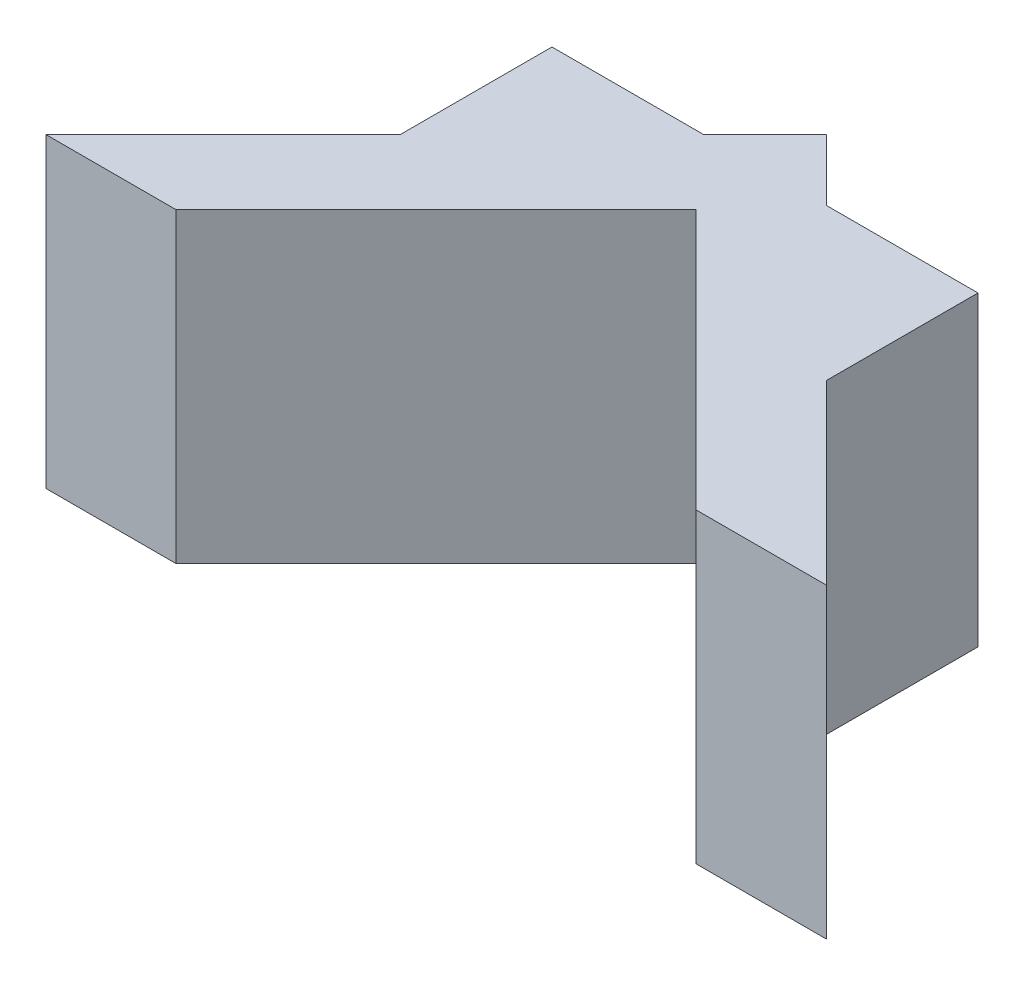
SolidWorks part; units mm, degrees
ref_plane "정면" through (0, 0, 0) normal (0, 0, 1) x (1, 0, 0)
ref_plane "윗면" through (0, 0, 0) normal (0, 1, 0) x (1, 0, 0)
ref_plane "우측면" through (0, 0, 0) normal (1, 0, 0) x (0, 0, -1)
sketch "스케치2" plane through (0, 0, 0) normal (0, 1, 0) x (1, 0, 0)
  line L0 (8.4853, -8.4853) -> (0, 0)
  line L1 (0, 0) -> (-8.4853, -8.4853)
  line L3 (-12.7279, -8.4853) -> (0, 4.2426)
  line L4 (0, 4.2426) -> (12.7279, -8.4853)
  line L6 (-12.7279, -8.4853) -> (-8.4853, -8.4853)
  line L7 (12.7279, -8.4853) -> (8.4853, -8.4853)
  dimension "D1" = 3
  dimension "D6" = 135
extrude "보스-돌출1" add sketch "스케치2" along normal blind 10
sketch "스케치3" plane through (0, 10, 0) normal (0, 1, 0) x (1, 0, 0)
  line L0 (-6.9497, -2.7071) -> (-2, 2.2426)
  line L1 (0, 4.2426) -> (-12.7279, -8.4853) construction
  line L3 (12.7279, -8.4853) -> (0, 4.2426) construction
  line L4 (2, 2.2426) -> (6.9497, -2.7071)
  line L5 (-6.9497, -2.7071) -> (-6.9497, 2.2426)
  line L6 (-6.9497, 2.2426) -> (-2, 2.2426)
  line L7 (2, 2.2426) -> (6.9497, 2.2426)
  line L8 (6.9497, 2.2426) -> (6.9497, -2.7071)
  dimension "D1" = 4
  dimension "D2" = 0
  dimension "D3" = 7
  dimension "D4" = 7
extrude "보스-돌출2" add sketch "스케치3" against normal up to surface (10 mm away) contours L4 L8 L7 | L6 L0 L5 up to face at (0, 0, 4.9497)
sketch "스케치5" plane through (0, 0, -2.2426) normal (0, 0, -1) x (-1, 0, 0)
  line L0 (-2, 0) -> (-6.9497, 0) construction
  line L1 (-6.14, 7.57) -> (-3, 7.57)
  line L2 (-6.14, 7.57) -> (-6.14, 2.43)
  line L3 (-6.14, 2.43) -> (-3, 2.43)
  line L4 (-3, 7.57) -> (-3, 2.43)
  line L5 (-6.14, 7.57) -> (-3, 2.43) construction
  line L6 (-6.14, 2.43) -> (-3, 7.57) construction
  line L7 (3, 7.57) -> (6.14, 7.57)
  line L8 (3, 7.57) -> (3, 2.43)
  line L9 (3, 2.43) -> (6.14, 2.43)
  line L10 (6.14, 7.57) -> (6.14, 2.43)
  line L11 (3, 7.57) -> (6.14, 2.43) construction
  line L12 (3, 2.43) -> (6.14, 7.57) construction
  line L13 (0, 9.7733) -> (0, 0) construction
  line L14 (6.9497, 0) -> (2, 0) construction
  point P0 (-4.57, 5)
  point P7 (4.57, 5)
  dimension "D1" = 6
  dimension "D2" = 3.14
  dimension "D3" = 5.14
  dimension "D4" = 5.14
  dimension "D5" = 3.14
  dimension "D6" = 2.43
  dimension "D7" = 3
  dimension "D8" = 2.43
extrude "컷-돌출1" cut sketch "스케치5" against normal blind 3
scale "축척1" scale about centroid uniform scaling yes scale factor 1.5
